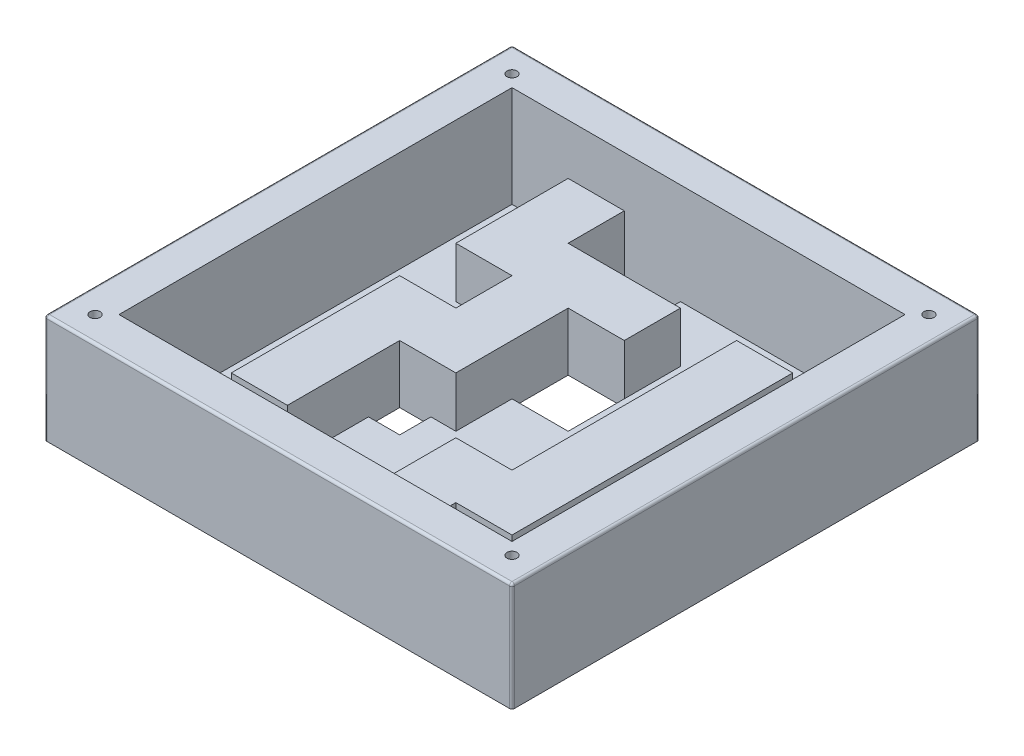
SolidWorks part; units mm, degrees
ref_plane "Plan de face" through (0, 0, 0) normal (0, 0, 1) x (1, 0, 0)
ref_plane "Plan de dessus" through (0, 0, 0) normal (0, 1, 0) x (1, 0, 0)
ref_plane "Plan de droite" through (0, 0, 0) normal (1, 0, 0) x (0, 0, -1)
sketch "Esquisse2" plane through (0, 0, 0) normal (0, 1, 0) x (1, 0, 0)
  line L1 (-92.5, 92.5) -> (92.5, 92.5)
  line L2 (-92.5, 92.5) -> (-92.5, -92.5)
  line L3 (-92.5, -92.5) -> (92.5, -92.5)
  line L4 (92.5, 92.5) -> (92.5, -92.5)
  dimension "D1" = 185
  dimension "D2" = 185
  dimension "D3" = 92.5
  dimension "D4" = 92.5
extrude "Boss.-Extru.1" add sketch "Esquisse2" against normal blind 3
sketch "Esquisse3" plane through (0, 0, 0) normal (0, 1, 0) x (1, 0, 0)
  line L0 (-77.77, 77.77) -> (77.77, 77.77)
  line L1 (-92.5, 92.5) -> (92.5, 92.5)
  line L2 (-92.5, 92.5) -> (-92.5, -92.5)
  line L3 (-92.5, -92.5) -> (92.5, -92.5)
  line L4 (92.5, 92.5) -> (92.5, -92.5)
  line L8 (77.77, 77.77) -> (77.77, -77.77)
  line L9 (-77.77, -77.77) -> (77.77, -77.77)
  line L10 (-77.77, 77.77) -> (-77.77, -77.77)
  dimension "D2" = 155.54
  dimension "D3" = 155.54
  dimension "D1" = 14.73
extrude "Boss.-Extru.2" add sketch "Esquisse3" along normal blind 40
sketch "Esquisse4" plane through (0, 0, 0) normal (0, 1, 0) x (1, 0, 0)
  line L0 (-55.55, 77.77) -> (-33.33, 77.77)
  line L1 (77.77, 77.77) -> (-77.77, 77.77) construction
  line L2 (-33.33, 77.77) -> (-33.33, 55.55)
  line L3 (-33.33, 55.55) -> (11.11, 55.55)
  line L4 (11.11, 55.55) -> (11.11, 33.33)
  line L5 (11.11, 33.33) -> (-11.11, 33.33)
  line L6 (-11.11, 33.33) -> (-11.11, -11.11)
  line L8 (-33.33, -11.11) -> (-33.33, -55.55)
  line L9 (-33.33, -55.55) -> (-55.55, -55.55)
  line L13 (-33.33, -11.11) -> (-11.11, -11.11)
  line L14 (-55.55, 77.77) -> (-55.55, 33.33)
  line L15 (-55.55, 33.33) -> (-33.33, 33.33)
  line L16 (-33.33, 33.33) -> (-33.33, 11.11)
  line L17 (-33.33, 11.11) -> (-55.55, 11.11)
  line L18 (-55.55, 11.11) -> (-55.55, -55.55)
  line L19 (-77.77, 77.77) -> (-77.77, -77.77) construction
  line L20 (-77.77, -77.77) -> (77.77, -77.77) construction
  line L21 (77.77, -77.77) -> (77.77, 77.77) construction
  line L22 (33.33, 55.55) -> (55.55, 55.55)
  line L23 (33.33, 55.55) -> (33.33, -33.33)
  line L25 (55.55, 55.55) -> (55.55, -55.55)
  line L28 (55.55, -55.55) -> (33.33, -55.55)
  line L30 (33.33, -33.33) -> (11.11, -33.33)
  line L32 (33.33, -77.77) -> (11.11, -77.77)
  line L33 (11.11, -33.33) -> (11.11, -77.77)
  line L34 (33.33, -55.55) -> (33.33, -77.77)
  line L35 (77.77, -77.77) -> (77.77, 77.77) construction
  dimension "D1" = 22.22
  dimension "D2" = 22.22
  dimension "D3" = 22.22
  dimension "D4" = 22.22
  dimension "D5" = 22.22
  dimension "D6" = 22.22
  dimension "D7" = 22.22
  dimension "D8" = 22.22
  dimension "D9" = 22.22
  dimension "D10" = 66.66
  dimension "D11" = 22.22
  dimension "D12" = 22.22
  dimension "D13" = 22.22
  dimension "D14" = 22.22
  dimension "D15" = 22.22
  dimension "D16" = 22.22
  dimension "D17" = 22.22
  dimension "D18" = 44.44
extrude "Boss.-Extru.3" add sketch "Esquisse4" along normal blind 20
sketch "Esquisse5" plane through (0, 0, 0) normal (0, 1, 0) x (1, 0, 0)
  line L0 (77.77, 77.77) -> (-33.33, 77.77) construction
  line L1 (-33.33, 55.55) -> (-11.11, 55.55)
  line L2 (-33.33, 55.55) -> (-33.33, 77.77)
  line L3 (-33.33, 77.77) -> (-11.11, 77.77)
  line L4 (-11.11, 55.55) -> (-11.11, 77.77)
  line L5 (-11.11, -11.11) -> (-11.11, 33.33) construction
  line L6 (-11.11, 33.33) -> (11.11, 33.33)
  line L7 (-11.11, 33.33) -> (-11.11, 11.11)
  line L8 (-11.11, 11.11) -> (11.11, 11.11)
  line L9 (11.11, 33.33) -> (11.11, 11.11)
  line L10 (11.11, 33.33) -> (11.11, 55.55) construction
  line L11 (-33.33, 11.11) -> (-55.55, 11.11) construction
  line L12 (33.33, -55.55) -> (55.55, -55.55) construction
  line L13 (-33.33, -11.11) -> (-20.98, -11.11)
  line L14 (-33.33, -11.11) -> (-33.33, -23.46)
  line L15 (-33.33, -23.46) -> (-20.98, -23.46)
  line L16 (-20.98, -11.11) -> (-20.98, -23.46)
  line L17 (-72.835, 28.395) -> (-60.485, 28.395)
  line L18 (-72.835, 28.395) -> (-72.835, 16.045)
  line L19 (-72.835, 16.045) -> (-60.485, 16.045)
  line L20 (-60.485, 28.395) -> (-60.485, 16.045)
  line L21 (-72.835, -60.485) -> (-60.485, -60.485)
  line L22 (-72.835, -60.485) -> (-72.835, -72.835)
  line L23 (-72.835, -72.835) -> (-60.485, -72.835)
  line L24 (-60.485, -60.485) -> (-60.485, -72.835)
  line L25 (60.485, -60.485) -> (72.835, -60.485)
  line L26 (60.485, -60.485) -> (60.485, -72.835)
  line L27 (60.485, -72.835) -> (72.835, -72.835)
  line L28 (72.835, -60.485) -> (72.835, -72.835)
  line L29 (11.11, -55.55) -> (-1.24, -55.55)
  line L30 (11.11, -55.55) -> (11.11, -43.2)
  line L31 (11.11, -43.2) -> (-1.24, -43.2)
  line L32 (-1.24, -55.55) -> (-1.24, -43.2)
  line L34 (11.11, -33.33) -> (11.11, -77.77) construction
  line L35 (-77.77, 77.77) -> (-77.77, -77.77) construction
  line L36 (-55.55, 33.33) -> (-33.33, 33.33) construction
  line L37 (-55.55, 77.77) -> (-55.55, 33.33) construction
  line L38 (-77.77, -77.77) -> (11.11, -77.77) construction
  line L39 (77.77, -77.77) -> (77.77, 77.77) construction
  dimension "D1" = 12.35
  dimension "D2" = 12.35
  dimension "D3" = 12.35
  dimension "D4" = 12.35
  dimension "D5" = 12.35
  dimension "D6" = 12.35
  dimension "D7" = 12.35
  dimension "D8" = 12.35
  dimension "D9" = 12.35
  dimension "D10" = 12.35
  dimension "D11" = 4.935
  dimension "D12" = 4.935
  dimension "D13" = 4.935
  dimension "D14" = 4.935
  dimension "D15" = 4.935
  dimension "D16" = 4.935
extrude "Enlèv. mat.-Extru.1" cut sketch "Esquisse5" against normal up to next
fillet "Congé1" radius 1 8 edges at (-92.5, 18.5, -92.5) (-92.5, 18.5, 92.5) (-92.5, 40, 0) (0, 40, 92.5) (0, 40, -92.5) (92.5, 40, 0) (92.5, 18.5, -92.5) (92.5, 18.5, 92.5)
sketch "Esquisse6" plane through (0, 40, 0) normal (0, 1, 0) x (1, 0, 0)
  line L0 (92.5, 91.5) -> (92.5, -91.5) construction
  line L1 (-91.5, 92.5) -> (91.5, 92.5) construction
  line L2 (91.5, -92.5) -> (-91.5, -92.5) construction
  line L3 (-92.5, -91.5) -> (-92.5, 91.5) construction
  circle A0 centre (-82.5, -82.5) radius 1
  circle A1 centre (82.5, -82.5) radius 1
  circle A2 centre (82.5, 82.5) radius 1
  circle A3 centre (-82.5, 82.5) radius 1
  dimension "D1" = 2
  dimension "D2" = 10
  dimension "D3" = 10
  dimension "D4" = 10
  dimension "D5" = 10
extrude "Enlèv. mat.-Extru.2" cut sketch "Esquisse6" against normal through all
sketch "Esquisse7" plane through (0, 40, 0) normal (0, 1, 0) x (1, 0, 0)
  circle A0 centre (-82.5, -82.5) radius 2
  circle A1 centre (-82.5, 82.5) radius 2
  circle A2 centre (82.5, 82.5) radius 2
  circle A3 centre (82.5, -82.5) radius 2
  dimension "D1" = 4
extrude "Enlèv. mat.-Extru.3" cut sketch "Esquisse7" against normal blind 41
